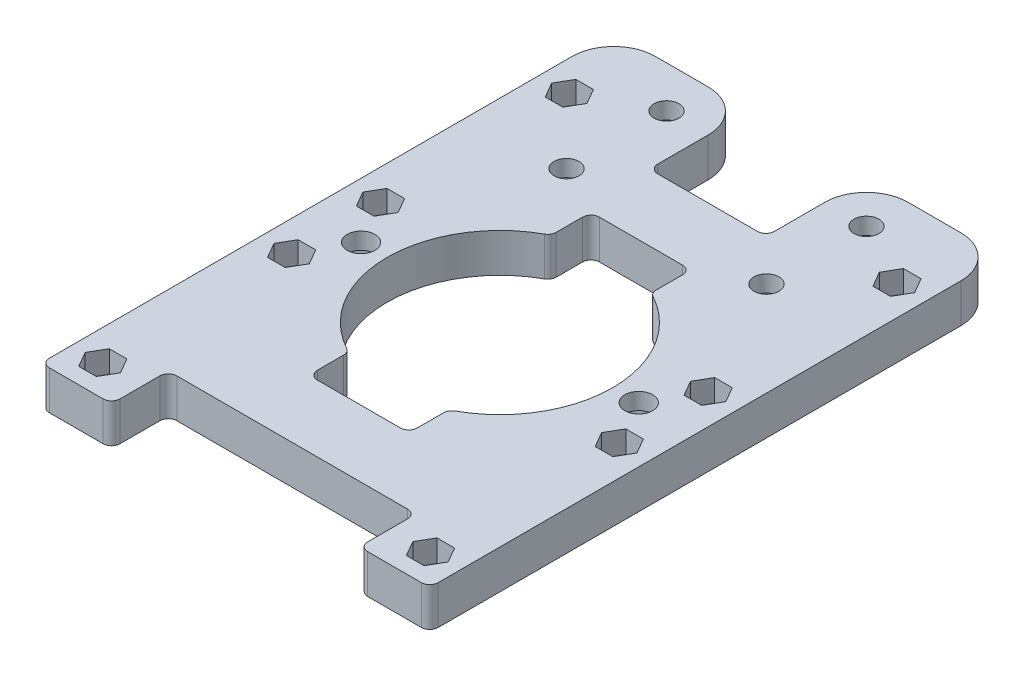
SolidWorks part; units mm, degrees
ref_plane "Front Plane" through (0, 0, 0) normal (0, 0, 1) x (1, 0, 0)
ref_plane "Top Plane" through (0, 0, 0) normal (0, 1, 0) x (1, 0, 0)
ref_plane "Right Plane" through (0, 0, 0) normal (1, 0, 0) x (0, 0, -1)
sketch "Sketch1" plane through (0, 0, 0) normal (0, 1, 0) x (1, 0, 0)
  line L0 (-29.5, 42) -> (-29.5, 8) construction
  line L1 (-29.5, -8) -> (-29.5, -42) construction
  line L2 (-35, 48) -> (-35, -46.101)
  line L3 (-33.476, -47.625) -> (-23.824, -47.625)
  line L4 (35, 48) -> (35, -46.101)
  line L5 (-10.5, 48) -> (-10.5, 38.924)
  line L6 (10.5, 48) -> (10.5, 38.924)
  line L7 (-29.5, 25) -> (-20.776, 25) construction
  line L8 (-8.976, 37.4) -> (8.976, 37.4)
  line L9 (-29.5, -25) -> (-20.776, -25) construction
  line L10 (0, 37.4) -> (0, 0) construction
  line L11 (0, 0) -> (0, -37.4) construction
  line L12 (-9, -19.1417) -> (-9, -23.876)
  line L13 (-7.476, 25.4) -> (7.476, 25.4)
  line L14 (-9, 23.876) -> (-9, 19.1417)
  line L15 (-7.476, -25.4) -> (7.476, -25.4)
  line L16 (9, 23.876) -> (9, 19.1417)
  line L17 (9, -19.1417) -> (9, -23.876)
  line L18 (23.824, -47.625) -> (33.476, -47.625)
  line L19 (-18, 55.5) -> (-27.5, 55.5)
  line L20 (-22.3, -46.101) -> (-22.3, -38.924)
  line L21 (-20.776, -37.4) -> (20.776, -37.4)
  line L22 (22.3, -46.101) -> (22.3, -38.924)
  line L23 (18, 55.5) -> (27.5, 55.5)
  arc A0 (-9.7898, 17.8063) -> (-9.7898, -17.8063) centre (0, 0) ccw
  arc A1 (-10.5, 48) -> (-18, 55.5) centre (-18, 48) ccw
  arc A2 (18, 55.5) -> (10.5, 48) centre (18, 48) ccw
  circle A3 centre (-18, 48) radius 2.25
  circle A4 centre (18, 48) radius 2.25
  circle A5 centre (-18, 30) radius 2.25
  circle A6 centre (18, 30) radius 2.25
  circle A7 centre (-29.5, 42) radius 2.25
  circle A8 centre (-29.5, 8) radius 2.25
  circle A9 centre (-29.5, -8) radius 2.25
  circle A10 centre (-29.5, -42) radius 2.25
  circle A11 centre (29.5, -8) radius 2.25
  circle A12 centre (29.5, -42) radius 2.25
  circle A13 centre (29.5, 42) radius 2.25
  circle A14 centre (29.5, 8) radius 2.25
  arc A15 (9.7898, -17.8063) -> (9.7898, 17.8063) centre (0, 0) ccw
  circle A16 centre (-25, 0) radius 2.5
  circle A17 centre (25, 0) radius 2.5
  arc A18 (35, 48) -> (27.5, 55.5) centre (27.5, 48) ccw
  arc A19 (-35, 48) -> (-27.5, 55.5) centre (-27.5, 48) cw
  arc A20 (-9, -23.876) -> (-7.476, -25.4) centre (-7.476, -23.876) ccw
  arc A21 (7.476, -25.4) -> (9, -23.876) centre (7.476, -23.876) ccw
  arc A22 (9.7898, -17.8063) -> (9, -19.1417) centre (10.524, -19.1417) ccw
  arc A23 (9, 19.1417) -> (9.7898, 17.8063) centre (10.524, 19.1417) ccw
  arc A24 (-9.7898, 17.8063) -> (-9, 19.1417) centre (-10.524, 19.1417) ccw
  arc A25 (-7.476, 25.4) -> (-9, 23.876) centre (-7.476, 23.876) ccw
  arc A26 (7.476, 25.4) -> (9, 23.876) centre (7.476, 23.876) cw
  arc A27 (10.5, 38.924) -> (8.976, 37.4) centre (8.976, 38.924) cw
  arc A28 (-10.5, 38.924) -> (-8.976, 37.4) centre (-8.976, 38.924) ccw
  arc A29 (-9, -19.1417) -> (-9.7898, -17.8063) centre (-10.524, -19.1417) ccw
  arc A30 (-35, -46.101) -> (-33.476, -47.625) centre (-33.476, -46.101) ccw
  arc A31 (-22.3, -38.924) -> (-20.776, -37.4) centre (-20.776, -38.924) cw
  arc A32 (-23.824, -47.625) -> (-22.3, -46.101) centre (-23.824, -46.101) ccw
  arc A33 (33.476, -47.625) -> (35, -46.101) centre (33.476, -46.101) ccw
  arc A34 (20.776, -37.4) -> (22.3, -38.924) centre (20.776, -38.924) cw
  arc A35 (23.824, -47.625) -> (22.3, -46.101) centre (23.824, -46.101) cw
  point P60 (-9, -25.4)
  point P63 (9, -25.4)
  point P66 (9, -18.2182)
  point P83 (-35, -47.625)
  point P90 (35, -47.625)
  dimension "D6" = 40.64
  dimension "D7" = 7.5
  dimension "D8" = 4.5
  dimension "D14" = 34
  dimension "D20" = 5
  dimension "D3" = 7.5
  dimension "D25" = 1.524
  dimension "D26" = 1.524
  dimension "D27" = 1.524
  dimension "D28" = 1.524
  dimension "D1" = 70
  dimension "D2" = 47.625
  dimension "D4" = 48
  dimension "D5" = 36
  dimension "D9" = 18
  dimension "D10" = 25
  dimension "D11" = 50
  dimension "D12" = 5.5
  dimension "D13" = 5.5
  dimension "D16" = 18
  dimension "D17" = 50.8
  dimension "D18" = 25
  dimension "D19" = 25
  dimension "D21" = 12
  dimension "D22" = 12
  dimension "D23" = 12.7
  dimension "D24" = 12.7
extrude "Boss-Extrude1" add sketch "Sketch1" along normal blind 7
sketch "Sketch2" plane through (0, 7, 0) normal (0, 1, 0) x (1, 0, 0)
  line L1 (-26.3246, 42) -> (-27.9123, 44.75)
  line L2 (-27.9123, 44.75) -> (-31.0877, 44.75)
  line L3 (-31.0877, 44.75) -> (-32.6754, 42)
  line L4 (-32.6754, 42) -> (-31.0877, 39.25)
  line L5 (-31.0877, 39.25) -> (-27.9123, 39.25)
  line L6 (-27.9123, 39.25) -> (-26.3246, 42)
  line L7 (26.3246, 42) -> (27.9123, 39.25)
  line L8 (27.9123, 39.25) -> (31.0877, 39.25)
  line L9 (31.0877, 39.25) -> (32.6754, 42)
  line L10 (32.6754, 42) -> (31.0877, 44.75)
  line L11 (31.0877, 44.75) -> (27.9123, 44.75)
  line L12 (27.9123, 44.75) -> (26.3246, 42)
  line L13 (26.3246, 8) -> (27.9123, 5.25)
  line L14 (27.9123, 5.25) -> (31.0877, 5.25)
  line L15 (31.0877, 5.25) -> (32.6754, 8)
  line L16 (32.6754, 8) -> (31.0877, 10.75)
  line L17 (31.0877, 10.75) -> (27.9123, 10.75)
  line L18 (27.9123, 10.75) -> (26.3246, 8)
  line L19 (26.3246, -8) -> (27.9123, -10.75)
  line L20 (27.9123, -10.75) -> (31.0877, -10.75)
  line L21 (31.0877, -10.75) -> (32.6754, -8)
  line L22 (32.6754, -8) -> (31.0877, -5.25)
  line L23 (31.0877, -5.25) -> (27.9123, -5.25)
  line L24 (27.9123, -5.25) -> (26.3246, -8)
  line L25 (26.3246, -42) -> (27.9123, -44.75)
  line L26 (27.9123, -44.75) -> (31.0877, -44.75)
  line L27 (31.0877, -44.75) -> (32.6754, -42)
  line L28 (32.6754, -42) -> (31.0877, -39.25)
  line L29 (31.0877, -39.25) -> (27.9123, -39.25)
  line L30 (27.9123, -39.25) -> (26.3246, -42)
  line L31 (-26.3246, -42) -> (-27.9123, -39.25)
  line L32 (-27.9123, -39.25) -> (-31.0877, -39.25)
  line L33 (-31.0877, -39.25) -> (-32.6754, -42)
  line L34 (-32.6754, -42) -> (-31.0877, -44.75)
  line L35 (-31.0877, -44.75) -> (-27.9123, -44.75)
  line L36 (-27.9123, -44.75) -> (-26.3246, -42)
  line L37 (-26.3246, -8) -> (-27.9123, -5.25)
  line L38 (-27.9123, -5.25) -> (-31.0877, -5.25)
  line L39 (-31.0877, -5.25) -> (-32.6754, -8)
  line L40 (-32.6754, -8) -> (-31.0877, -10.75)
  line L41 (-31.0877, -10.75) -> (-27.9123, -10.75)
  line L42 (-27.9123, -10.75) -> (-26.3246, -8)
  line L43 (-26.3246, 8) -> (-27.9123, 10.75)
  line L44 (-27.9123, 10.75) -> (-31.0877, 10.75)
  line L45 (-31.0877, 10.75) -> (-32.6754, 8)
  line L46 (-32.6754, 8) -> (-31.0877, 5.25)
  line L47 (-31.0877, 5.25) -> (-27.9123, 5.25)
  line L48 (-27.9123, 5.25) -> (-26.3246, 8)
  circle A0 centre (-29.5, 42) radius 2.75 construction
  circle A1 centre (29.5, 42) radius 2.75 construction
  circle A2 centre (29.5, 8) radius 2.75 construction
  circle A3 centre (29.5, -8) radius 2.75 construction
  circle A4 centre (29.5, -42) radius 2.75 construction
  circle A5 centre (-29.5, -42) radius 2.75 construction
  circle A6 centre (-29.5, -8) radius 2.75 construction
  circle A7 centre (-29.5, 8) radius 2.75 construction
  dimension "D1" = 5.5
extrude "Cut-Extrude1" cut sketch "Sketch2" against normal blind 4
sketch "Sketch3" plane through (0, 0, 0) normal (0, -1, 0) x (1, 0, 0)
  line L1 (-18, -33.1754) -> (-15.25, -31.5877)
  line L2 (-15.25, -31.5877) -> (-15.25, -28.4123)
  line L3 (-15.25, -28.4123) -> (-18, -26.8246)
  line L4 (-18, -26.8246) -> (-20.75, -28.4123)
  line L5 (-20.75, -28.4123) -> (-20.75, -31.5877)
  line L6 (-20.75, -31.5877) -> (-18, -33.1754)
  line L7 (-18, -51.1754) -> (-15.25, -49.5877)
  line L8 (-15.25, -49.5877) -> (-15.25, -46.4123)
  line L9 (-15.25, -46.4123) -> (-18, -44.8246)
  line L10 (-18, -44.8246) -> (-20.75, -46.4123)
  line L11 (-20.75, -46.4123) -> (-20.75, -49.5877)
  line L12 (-20.75, -49.5877) -> (-18, -51.1754)
  line L13 (18, -51.1754) -> (20.75, -49.5877)
  line L14 (20.75, -49.5877) -> (20.75, -46.4123)
  line L15 (20.75, -46.4123) -> (18, -44.8246)
  line L16 (18, -44.8246) -> (15.25, -46.4123)
  line L17 (15.25, -46.4123) -> (15.25, -49.5877)
  line L18 (15.25, -49.5877) -> (18, -51.1754)
  line L19 (18, -33.1754) -> (20.75, -31.5877)
  line L20 (20.75, -31.5877) -> (20.75, -28.4123)
  line L21 (20.75, -28.4123) -> (18, -26.8246)
  line L22 (18, -26.8246) -> (15.25, -28.4123)
  line L23 (15.25, -28.4123) -> (15.25, -31.5877)
  line L24 (15.25, -31.5877) -> (18, -33.1754)
  circle A0 centre (-18, -30) radius 2.75 construction
  circle A1 centre (-18, -48) radius 2.75 construction
  circle A2 centre (18, -48) radius 2.75 construction
  circle A3 centre (18, -30) radius 2.75 construction
  dimension "D1" = 5.5
extrude "Cut-Extrude2" cut sketch "Sketch3" against normal blind 4
sketch "Sketch4" plane through (0, 0, 0) normal (0, -1, 0) x (1, 0, 0)
  line L1 (-25, -4.3301) -> (-21.25, -2.1651)
  line L2 (-21.25, -2.1651) -> (-21.25, 2.1651)
  line L3 (-21.25, 2.1651) -> (-25, 4.3301)
  line L4 (-25, 4.3301) -> (-28.75, 2.1651)
  line L5 (-28.75, 2.1651) -> (-28.75, -2.1651)
  line L6 (-28.75, -2.1651) -> (-25, -4.3301)
  line L7 (25, -4.3301) -> (28.75, -2.1651)
  line L8 (28.75, -2.1651) -> (28.75, 2.1651)
  line L9 (28.75, 2.1651) -> (25, 4.3301)
  line L10 (25, 4.3301) -> (21.25, 2.1651)
  line L11 (21.25, 2.1651) -> (21.25, -2.1651)
  line L12 (21.25, -2.1651) -> (25, -4.3301)
  circle A0 centre (-25, 0) radius 3.75 construction
  circle A1 centre (25, 0) radius 3.75 construction
  dimension "D1" = 7.5
extrude "Cut-Extrude3" cut sketch "Sketch4" against normal blind 4
